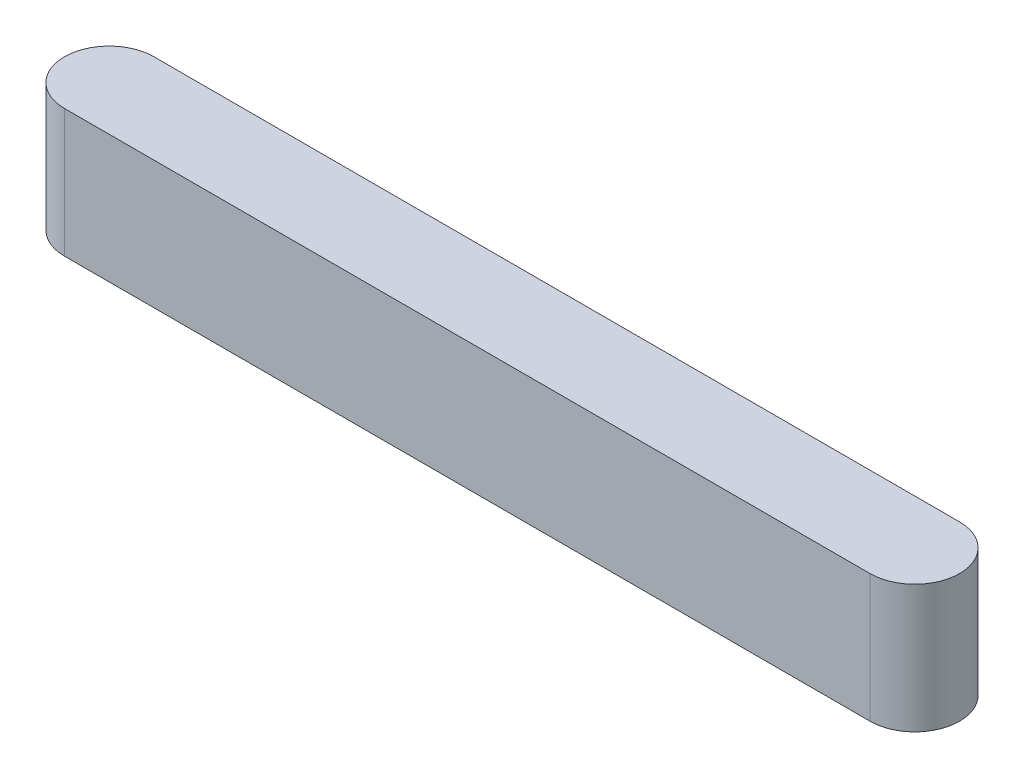
SolidWorks part; units mm, degrees
material "6061-T6 (SS)"
ref_plane "Front Plane" through (0, 0, 0) normal (0, 0, 1) x (1, 0, 0)
ref_plane "Top Plane" through (0, 0, 0) normal (0, 1, 0) x (1, 0, 0)
ref_plane "Right Plane" through (0, 0, 0) normal (1, 0, 0) x (0, 0, -1)
sketch "Sketch1" plane through (0, 0, 0) normal (0, 1, 0) x (1, 0, 0)
  line L1 (-9, 1) -> (9, 1)
  line L3 (-9, -1) -> (9, -1)
  line L5 (-9, 1) -> (9, -1) construction
  line L6 (-9, -1) -> (9, 1) construction
  arc A0 (-9, 1) -> (-9, -1) centre (-9, 0) ccw
  arc A1 (9, -1) -> (9, 1) centre (9, 0) ccw
  point P0 (0, 0)
  dimension "D1" = 2
  dimension "D2" = 20
extrude "Boss-Extrude1" add sketch "Sketch1" along normal blind 2.8575
